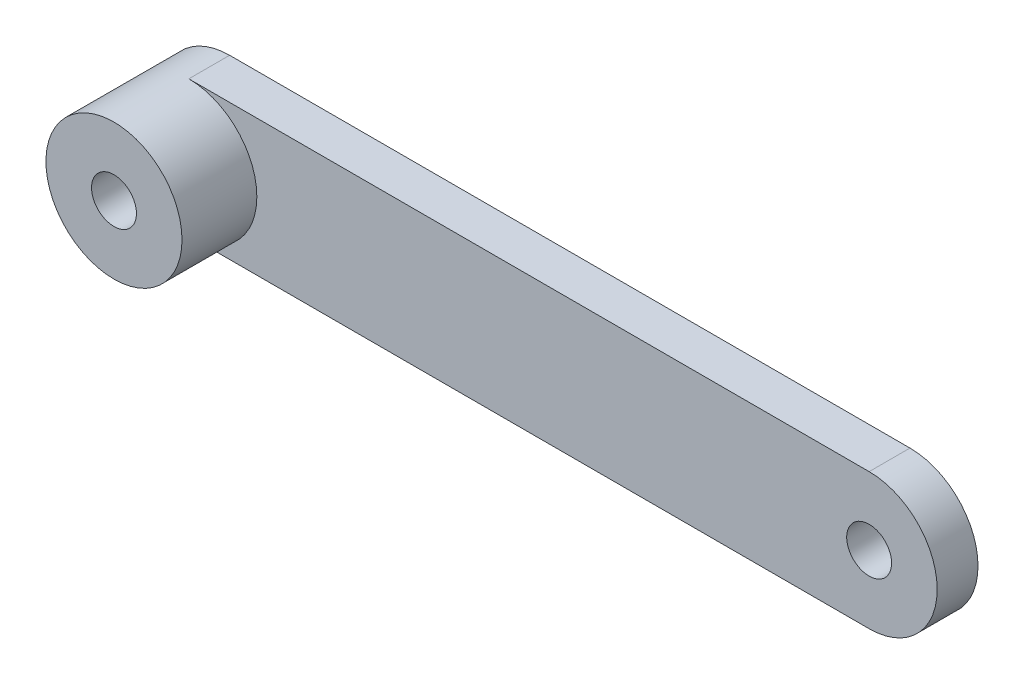
SolidWorks part; units mm, degrees
ref_plane "前基準面" through (0, 0, 0) normal (0, 0, 1) x (1, 0, 0)
ref_plane "上基準面" through (0, 0, 0) normal (0, 1, 0) x (1, 0, 0)
ref_plane "右基準面" through (0, 0, 0) normal (1, 0, 0) x (0, 0, -1)
sketch "草圖1" plane through (0, 0, 0) normal (0, 0, 1) x (1, 0, 0)
  line L0 (0, 0) -> (50, 0) construction
  line L1 (0, 5) -> (50, 5)
  line L2 (0, -5) -> (50, -5)
  circle A0 centre (0, 0) radius 1.65
  circle A1 centre (50, 0) radius 1.65
  arc A2 (0, 5) -> (0, -5) centre (0, 0) ccw
  arc A3 (50, -5) -> (50, 5) centre (50, 0) ccw
  point P5 (25, 0)
  dimension "D3" = 3.3
  dimension "D1" = 50
  dimension "D2" = 10
extrude "填料-伸長1" add sketch "草圖1" along normal blind 3
sketch "草圖2" plane through (0, 0, 3) normal (0, 0, 1) x (1, 0, 0)
  circle A0 centre (0, 0) radius 5
  circle A1 centre (0, 0) radius 1.65
  circle A2 centre (0, 0) radius 1.65 construction
  arc A3 (0, 5) -> (0, -5) centre (0, 0) ccw construction
extrude "填料-伸長2" add sketch "草圖2" along normal blind 5.5
